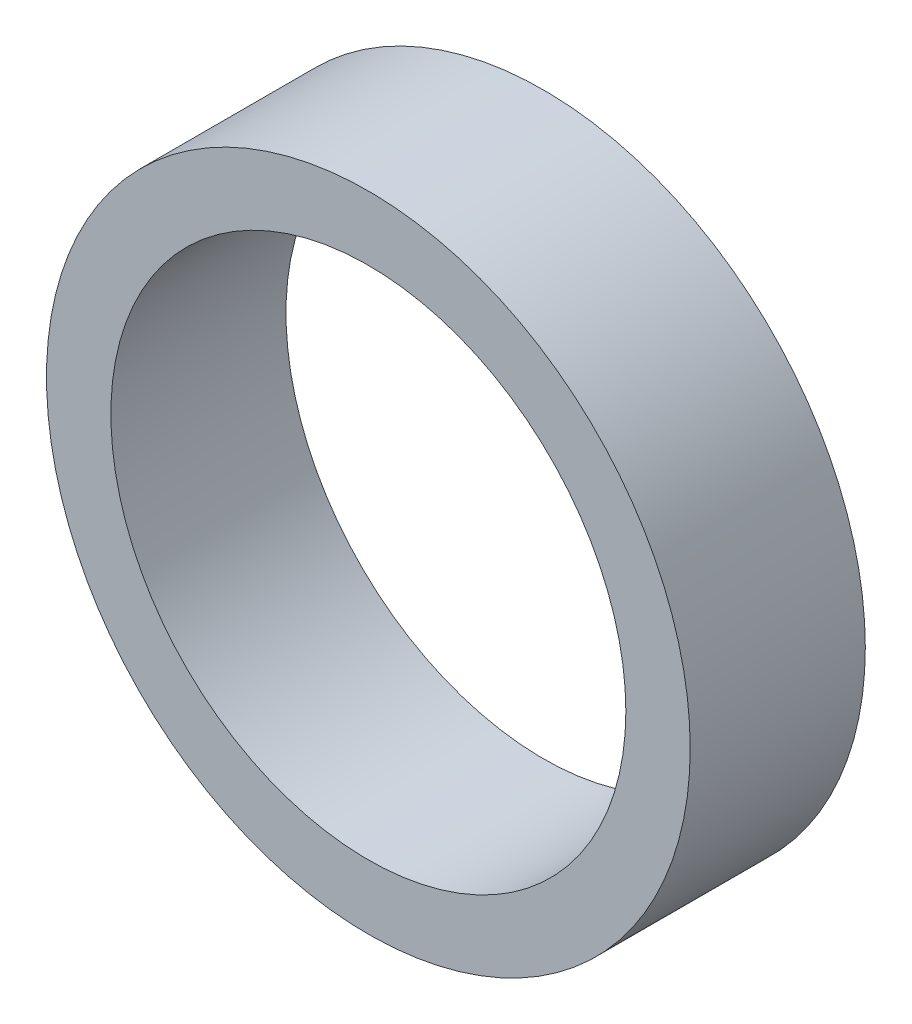
SolidWorks part; units mm, degrees
ref_plane "Front Plane" through (0, 0, 0) normal (0, 0, 1) x (1, 0, 0)
ref_plane "Top Plane" through (0, 0, 0) normal (0, 1, 0) x (1, 0, 0)
ref_plane "Right Plane" through (0, 0, 0) normal (1, 0, 0) x (0, 0, -1)
sketch "Sketch1" plane through (0, 0, 0) normal (0, 0, 1) x (1, 0, 0)
  circle A0 centre (0, 0) radius 3.175
  circle A1 centre (0, 0) radius 3.9688
extrude "Extrude1" add sketch "Sketch1" along normal blind 2.159
